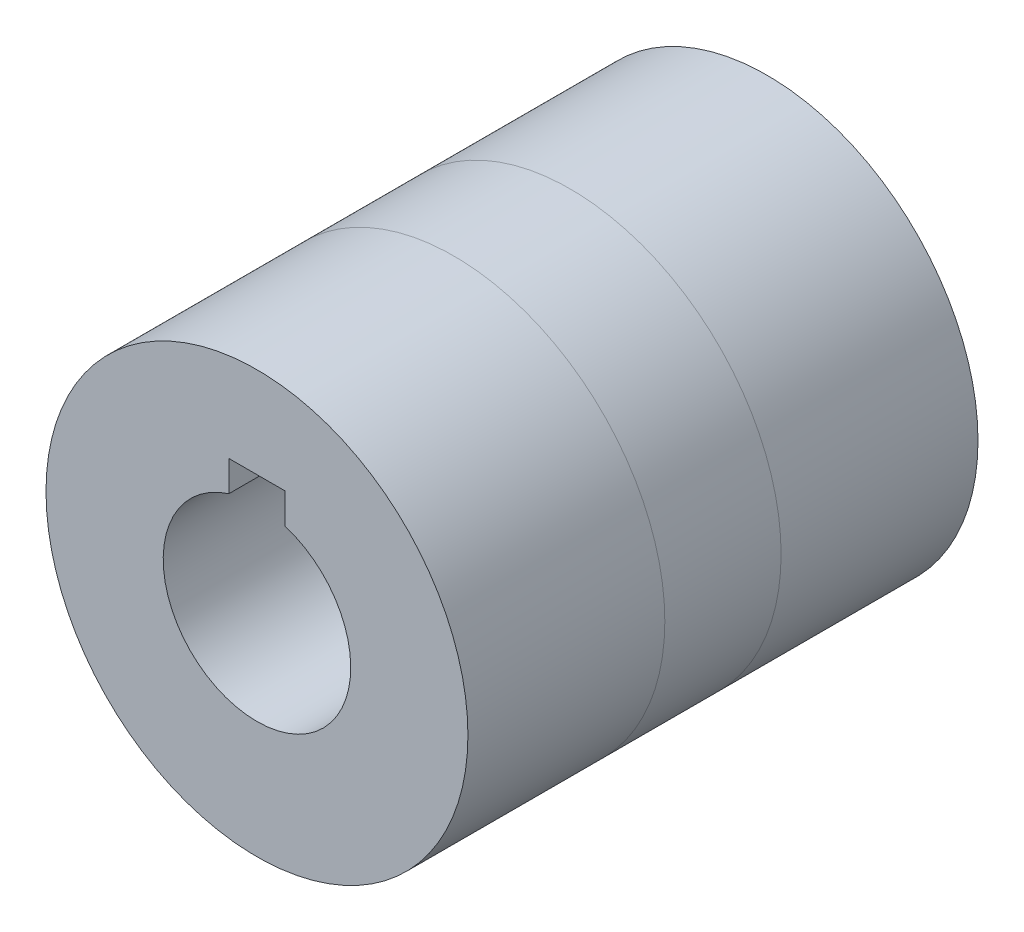
SolidWorks part; units mm, degrees
ref_plane "前视基准面" through (0, 0, 0) normal (0, 0, 1) x (1, 0, 0)
ref_plane "上视基准面" through (0, 0, 0) normal (0, 1, 0) x (1, 0, 0)
ref_plane "右视基准面" through (0, 0, 0) normal (1, 0, 0) x (0, 0, -1)
sketch "草图1" plane through (0, 0, 0) normal (0, 0, 1) x (1, 0, 0)
  circle A0 centre (0, 0) radius 10
  circle A1 centre (0, 0) radius 22.5
  dimension "D1" = 20
  dimension "D2" = 45
extrude "凸台-拉伸1" add sketch "草图1" along normal mid plane 12.4
sketch "草图3" plane through (0, 0, 6.2) normal (0, 0, 1) x (1, 0, 0)
  circle A1 centre (0, 0) radius 22.5
  circle A2 centre (0, 0) radius 22.5
  circle A3 centre (0, 0) radius 10 construction
  circle A4 centre (0, 0) radius 10
  dimension "D1" = 0
extrude "凸台-拉伸2" add sketch "草图3" along normal blind 21 separate body
sketch "草图4" plane through (0, 0, -6.2) normal (0, 0, -1) x (-1, 0, 0)
  circle A0 centre (0, 0) radius 22.5 construction
  circle A1 centre (0, 0) radius 10 construction
  circle A2 centre (0, 0) radius 10
  circle A3 centre (0, 0) radius 22.5
extrude "凸台-拉伸3" add sketch "草图4" along normal blind 21 separate body
sketch "草图6" plane through (0, 0, 27.2) normal (0, 0, 1) x (1, 0, 0)
  line L0 (0, 10) -> (0, 0) construction
  line L1 (3, 7.2) -> (-3, 7.2)
  line L2 (3, 7.2) -> (3, 12.8)
  line L3 (3, 12.8) -> (-3, 12.8)
  line L4 (-3, 7.2) -> (-3, 12.8)
  line L5 (3, 7.2) -> (-3, 12.8) construction
  line L6 (3, 12.8) -> (-3, 7.2) construction
  circle A0 centre (0, 0) radius 10 construction
  circle A1 centre (0, 0) radius 10 construction
  point P0 (0, 10)
  dimension "D1" = 6
  dimension "D2" = 12.8
extrude "切除-拉伸1" cut sketch "草图6" against normal through all
